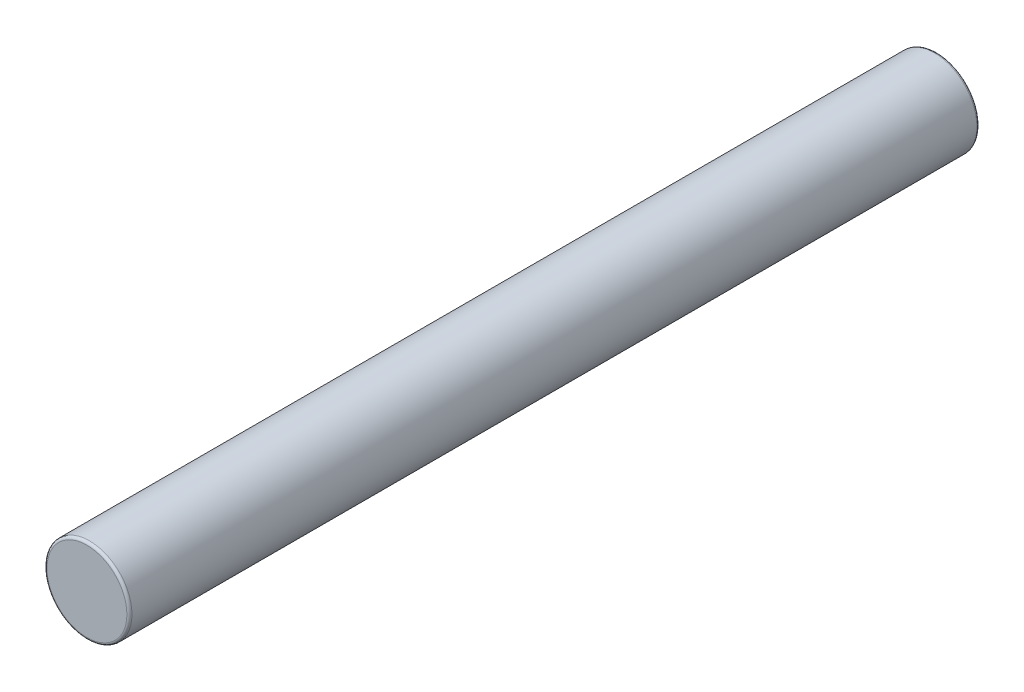
SolidWorks part; units mm, degrees
ref_plane "前视基准面" through (0, 0, 0) normal (0, 0, 1) x (1, 0, 0)
ref_plane "上视基准面" through (0, 0, 0) normal (0, 1, 0) x (1, 0, 0)
ref_plane "右视基准面" through (0, 0, 0) normal (1, 0, 0) x (0, 0, -1)
other "Configuration Table"
sketch "Sketch1" plane through (0, 0, 0) normal (0, 0, 1) x (1, 0, 0)
  circle A0 centre (0, 0) radius 5
  dimension "D1" = 10
extrude "Boss-Extrude1" add sketch "Sketch1" along normal mid plane 100
fillet "Fillet1" radius 0.3 2 edges at (5, 0, -50) (5, 0, 50)
